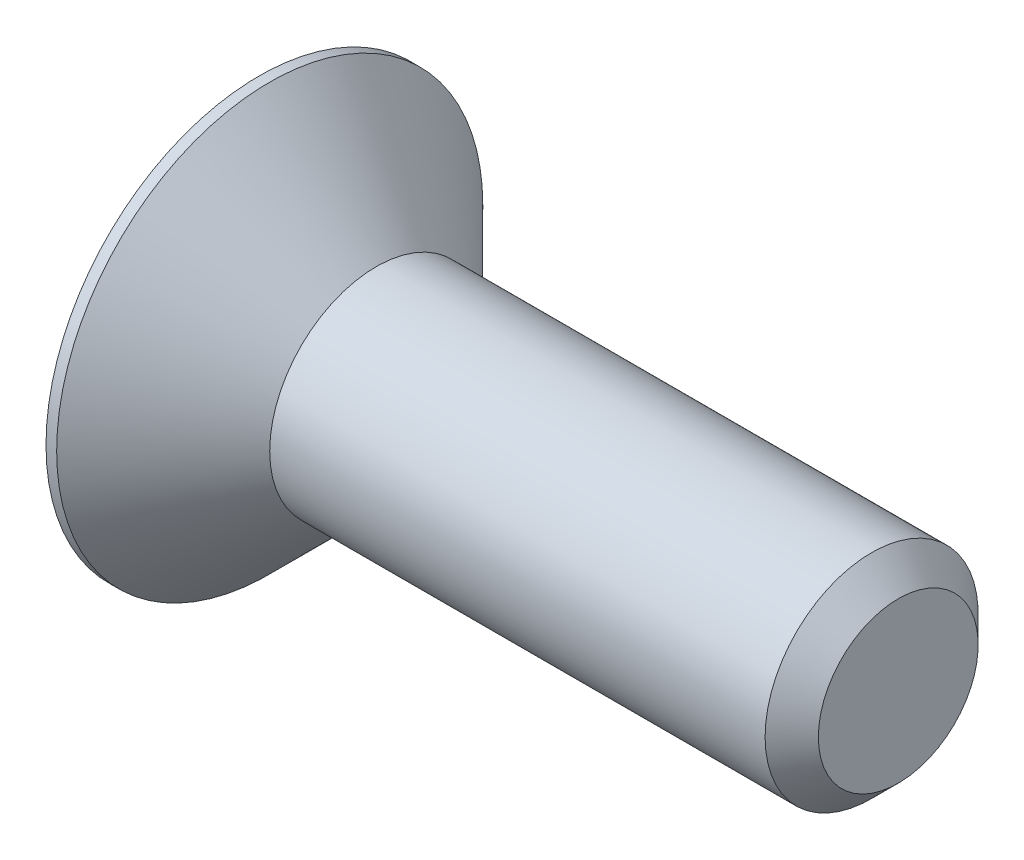
SolidWorks part; units mm, degrees
ref_plane "Front Plane" through (0, 0, 0) normal (0, 0, 1) x (1, 0, 0)
ref_plane "Top Plane" through (0, 0, 0) normal (0, 1, 0) x (1, 0, 0)
ref_plane "Right Plane" through (0, 0, 0) normal (1, 0, 0) x (0, 0, -1)
sketch "Sketch2" plane through (0, 0, 0) normal (0, 0, 1) x (1, 0, 0)
  line L0 (0, 0) -> (0, 2)
  line L1 (0, 2) -> (0.1, 2)
  line L2 (0.1, 2) -> (1.1, 1)
  line L3 (1.1, 1) -> (5.75, 1)
  line L4 (5.75, 1) -> (6, 0.75)
  line L5 (6, 0.75) -> (6, 0)
  line L6 (6, 0) -> (0, 0)
  line L7 (-2.2818, 0) -> (8.0811, 0) construction
  dimension "D1" = 4
  dimension "D2" = 0.1
  dimension "D3" = 45
  dimension "D4" = 6
  dimension "D5" = 0.25
  dimension "D6" = 2
revolve "Revolve1" add sketch "Sketch2" angle 360 about L7
sketch "Sketch3" plane through (0, 0, 0) normal (-1, 0, 0) x (0, 0, 1)
  line L1 (0.433, -0.75) -> (0.866, 0)
  line L2 (0.866, 0) -> (0.433, 0.75)
  line L3 (0.433, 0.75) -> (-0.433, 0.75)
  line L4 (-0.433, 0.75) -> (-0.866, 0)
  line L5 (-0.866, 0) -> (-0.433, -0.75)
  line L6 (-0.433, -0.75) -> (0.433, -0.75)
  circle A0 centre (0, 0) radius 0.75 construction
  dimension "D1" = 1.5
extrude "Cut-Extrude1" cut sketch "Sketch3" against normal blind 0.8
